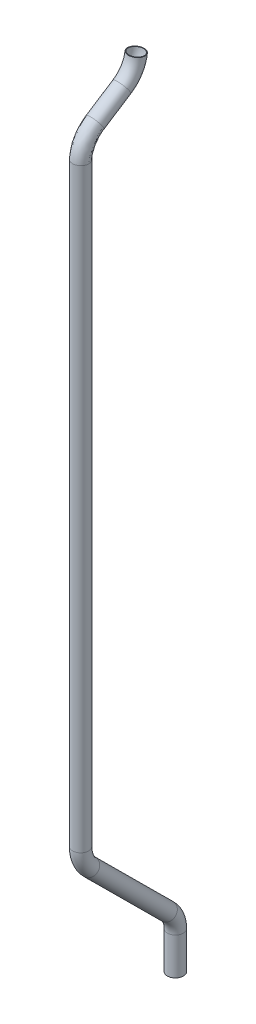
SolidWorks part; units mm, degrees
ref_plane "Front Plane" through (0, 0, 0) normal (0, 0, 1) x (1, 0, 0)
ref_plane "Top Plane" through (0, 0, 0) normal (0, 1, 0) x (1, 0, 0)
ref_plane "Right Plane" through (0, 0, 0) normal (1, 0, 0) x (0, 0, -1)
sketch "Sketch1" plane through (0, 0, 0) normal (0, 1, 0) x (1, 0, 0)
  circle A0 centre (0, 0) radius 9.525
  circle A1 centre (0, 0) radius 8.763
  dimension "D1" = 19.05
  dimension "D2" = 17.526
sketch "Sketch4" plane through (0, 0, 0) normal (1, 0, 0) x (0, 0, -1)
  line L0 (0, 0) -> (0, 44.45)
  line L1 (-9.365, 66.966) -> (-102.1311, 159.1924)
  line L2 (0, 44.45) -> (0, 66.966) construction
  line L3 (0, 66.966) -> (-9.365, 66.966) construction
  line L4 (-9.365, 66.966) -> (0, 79.2813) construction
  line L5 (-113.369, 186.2117) -> (-113.369, 897.4117)
  line L6 (-96.0184, 927.197) -> (-64.0226, 947.8823)
  arc A0 (0, 44.45) -> (-9.365, 66.966) centre (-31.75, 44.45) ccw
  arc A1 (-102.1311, 159.1924) -> (-113.369, 186.2117) centre (-75.269, 186.2117) cw
  arc A2 (-113.369, 897.4117) -> (-96.0184, 927.197) centre (-75.3332, 895.2012) cw
  arc A3 (-64.0226, 947.8823) -> (-46.8562, 975.5348) centre (-84.7079, 979.8781) ccw
  dimension "D1" = 31.75
  dimension "D3" = 130.81
  dimension "D4" = 38.1
  dimension "D5" = 711.2
  dimension "D6" = 38.1
  dimension "D8" = 38.1
  dimension "D2" = 44.45
  dimension "D7" = 38.1
sweep "Sweep1" add profiles "Sketch1" path "Sketch4"
